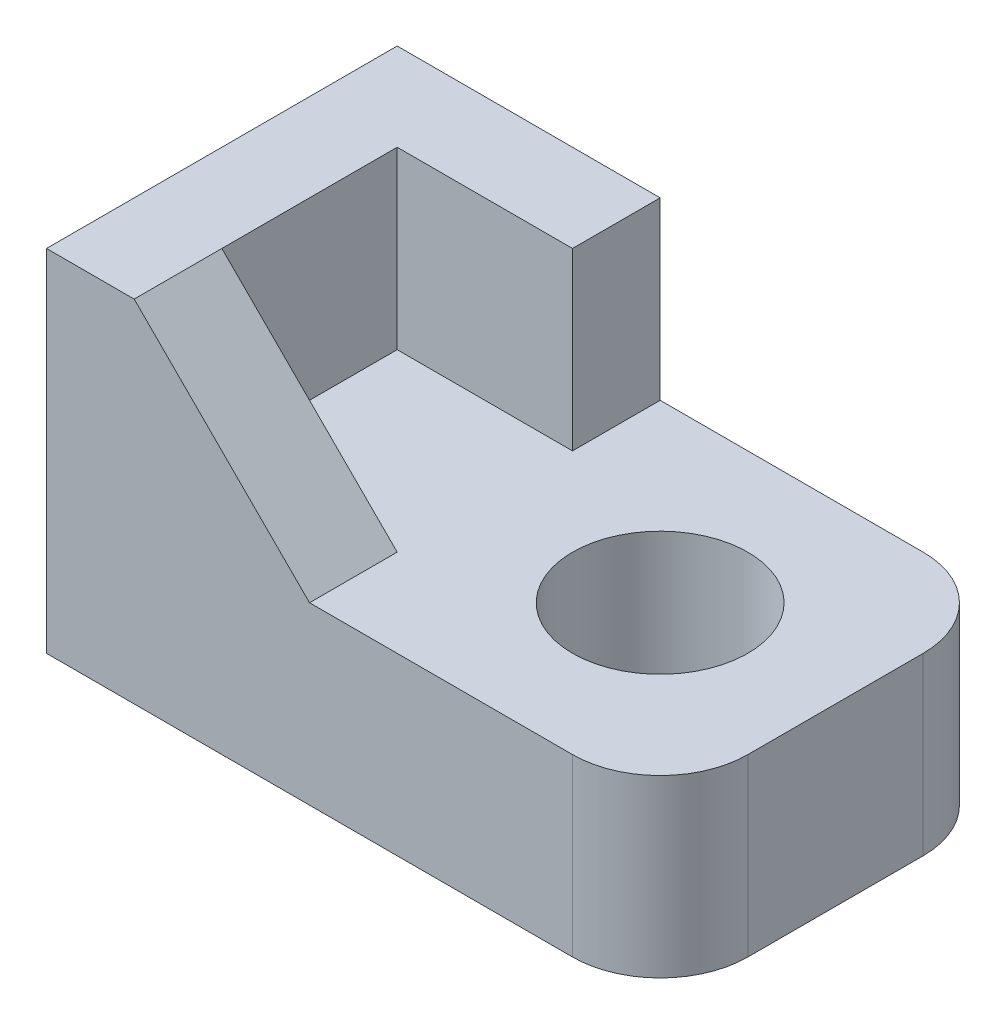
SolidWorks part; units mm, degrees
ref_plane "前基準面" through (0, 0, 0) normal (0, 0, 1) x (1, 0, 0)
ref_plane "上基準面" through (0, 0, 0) normal (0, 1, 0) x (1, 0, 0)
ref_plane "右基準面" through (0, 0, 0) normal (1, 0, 0) x (0, 0, -1)
sketch "草圖1" plane through (0, 0, 0) normal (0, 1, 0) x (1, 0, 0)
  line L0 (0, -13.2295) -> (0, 13.2295) construction
  line L1 (0, -2) -> (0, 2)
  line L2 (0, 2) -> (6, 2)
  line L3 (7, 1) -> (7, 0)
  line L4 (0, 0) -> (41.0198, 0) construction
  line L5 (5, 3.7564) -> (5, -13.1275) construction
  line L6 (5, -3.7564) -> (5, 13.1275) construction
  line L7 (0, -2) -> (6, -2)
  line L8 (7, 0) -> (7, -1)
  circle A0 centre (5, 0) radius 1
  arc A1 (7, 1) -> (6, 2) centre (6, 1) ccw
  arc A2 (7, -1) -> (6, -2) centre (6, -1) cw
  point P13 (7, 2)
  point P21 (7, -2)
  dimension "D4" = 2
  dimension "D5" = 1
  dimension "D1" = 2
  dimension "D2" = 7
  dimension "D3" = 2
extrude "填料-伸長1" add sketch "草圖1" along normal blind 2
sketch "草圖4" plane through (0, 0, 0) normal (0, 1, 0) x (1, 0, 0)
  line L0 (0, 0) -> (40.3797, 0) construction
  line L1 (0, 2) -> (0, -2) construction
  line L2 (0, 0) -> (0, 2)
  line L3 (0, 2) -> (3, 2)
  line L4 (6, 2) -> (0, 2) construction
  line L5 (3, 2) -> (3, 1)
  line L6 (3, 1) -> (1, 1)
  line L7 (1, 1) -> (1, -1)
  line L8 (1, -1) -> (3, -1)
  line L9 (3, -1) -> (3, -2)
  line L10 (0, -2) -> (6, -2) construction
  line L11 (3, -2) -> (0, -2)
  line L12 (0, -2) -> (0, 0)
  dimension "D1" = 3
  dimension "D2" = 1
  dimension "D3" = 2
  dimension "D4" = 2
  dimension "D5" = 2
extrude "填料-伸長2" add sketch "草圖4" along normal blind 4 contours L12 L2 L3 L5 L6 L7 L8 L9 L11
sketch "草圖5" plane through (0, 0, 2) normal (0, 0, 1) x (1, 0, 0)
  line L0 (3, 2) -> (1, 4)
  line L1 (3, 4) -> (0, 4) construction
  line L2 (1, 4) -> (3, 4)
  line L3 (3, 4) -> (3, 2)
  dimension "D1" = 2
extrude "除料-伸長1" cut sketch "草圖5" against normal blind 1
